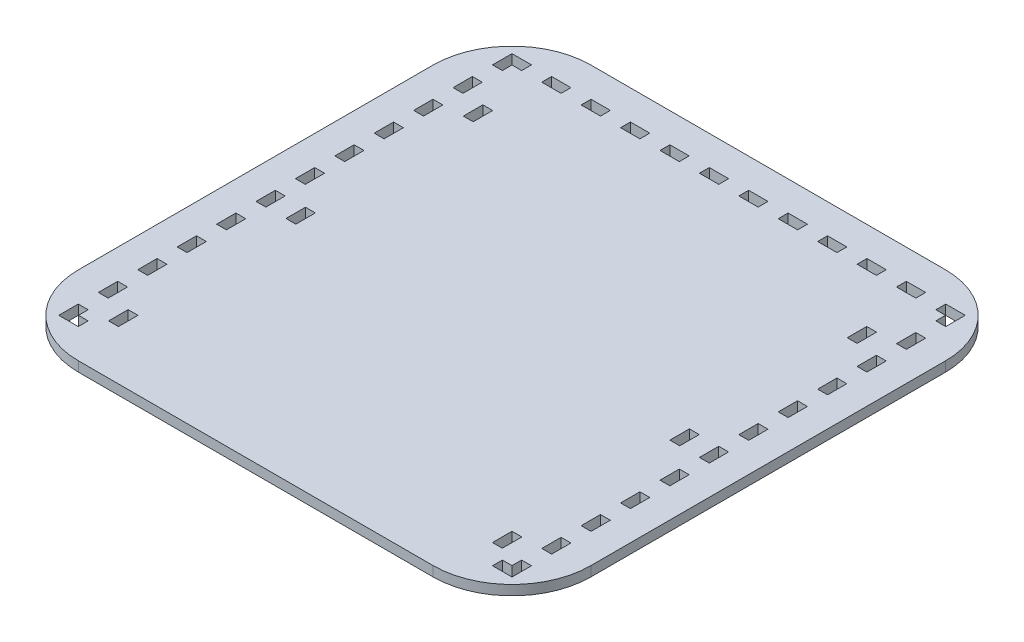
SolidWorks part; units mm, degrees
ref_plane "Front Plane" through (0, 0, 0) normal (0, 0, 1) x (1, 0, 0)
ref_plane "Top Plane" through (0, 0, 0) normal (0, 1, 0) x (1, 0, 0)
ref_plane "Right Plane" through (0, 0, 0) normal (1, 0, 0) x (0, 0, -1)
sketch "Sketch1" plane through (0, 0, 0) normal (0, 1, 0) x (1, 0, 0)
  line L0 (133.477, -292.1) -> (133.477, 0) construction
  line L1 (-6.223, -241.173) -> (-12.573, -241.173)
  line L2 (-6.223, -228.727) -> (-6.223, -241.173)
  line L3 (-12.573, -228.727) -> (-6.223, -228.727)
  line L4 (-12.573, -241.173) -> (-12.573, -254.127) construction
  line L5 (-6.223, -215.773) -> (-12.573, -215.773)
  line L6 (-6.223, -203.327) -> (-6.223, -215.773)
  line L7 (-12.573, -203.327) -> (-6.223, -203.327)
  line L8 (-12.573, -215.773) -> (-12.573, -228.727) construction
  line L9 (-6.223, -190.373) -> (-12.573, -190.373)
  line L10 (-6.223, -177.927) -> (-6.223, -190.373)
  line L11 (-12.573, -177.927) -> (-6.223, -177.927)
  line L12 (-12.573, -190.373) -> (-12.573, -203.327) construction
  line L13 (-6.223, -164.973) -> (-12.573, -164.973)
  line L14 (-6.223, -152.527) -> (-6.223, -164.973)
  line L15 (-12.573, -152.527) -> (-6.223, -152.527)
  line L16 (-12.573, -164.973) -> (-12.573, -177.927) construction
  line L17 (-6.223, -139.573) -> (-12.573, -139.573)
  line L18 (-6.223, -127.127) -> (-6.223, -139.573)
  line L19 (-12.573, -127.127) -> (-6.223, -127.127)
  line L20 (-12.573, -139.573) -> (-12.573, -152.527) construction
  line L21 (-6.223, -114.173) -> (-12.573, -114.173)
  line L22 (-6.223, -101.727) -> (-6.223, -114.173)
  line L23 (-12.573, -101.727) -> (-6.223, -101.727)
  line L24 (-12.573, -114.173) -> (-12.573, -127.127) construction
  line L25 (-6.223, -88.773) -> (-12.573, -88.773)
  line L26 (-6.223, -76.327) -> (-6.223, -88.773)
  line L27 (-12.573, -76.327) -> (-6.223, -76.327)
  line L28 (-12.573, -88.773) -> (-12.573, -101.727) construction
  line L29 (-6.223, -63.373) -> (-12.573, -63.373)
  line L30 (-6.223, -50.927) -> (-6.223, -63.373)
  line L31 (-12.573, -50.927) -> (-6.223, -50.927)
  line L32 (-12.573, -63.373) -> (-12.573, -76.327) construction
  line L33 (-6.223, -37.973) -> (-12.573, -37.973)
  line L34 (-6.223, -25.527) -> (-6.223, -37.973)
  line L35 (-12.573, -25.527) -> (-6.223, -25.527)
  line L36 (-12.573, -37.973) -> (-12.573, -50.927) construction
  line L37 (-6.223, -12.573) -> (-12.573, -12.573)
  line L38 (-6.223, -12.573) -> (-6.223, -6.35)
  line L39 (-6.223, -6.35) -> (0, -6.35)
  line L40 (-12.573, -12.573) -> (-12.573, -25.527) construction
  line L41 (0, -6.35) -> (0, 0)
  line L42 (273.177, -285.75) -> (273.177, -279.527)
  line L43 (273.177, -279.527) -> (279.527, -279.527)
  line L44 (279.527, -279.527) -> (279.527, -266.573) construction
  line L45 (279.527, -266.573) -> (273.177, -266.573)
  line L46 (273.177, -266.573) -> (273.177, -254.127)
  line L47 (273.177, -254.127) -> (279.527, -254.127)
  line L48 (279.527, -254.127) -> (279.527, -241.173) construction
  line L49 (12.954, -292.1) -> (12.954, -307.975) construction
  line L50 (279.527, -241.173) -> (273.177, -241.173)
  line L51 (-6.223, -279.527) -> (-6.223, -285.75)
  line L52 (-12.573, -279.527) -> (-6.223, -279.527)
  line L53 (-12.573, -266.573) -> (-12.573, -279.527) construction
  line L54 (-6.223, -266.573) -> (-12.573, -266.573)
  line L55 (-6.223, -254.127) -> (-6.223, -266.573)
  line L56 (-12.573, -254.127) -> (-6.223, -254.127)
  line L57 (273.177, -241.173) -> (273.177, -228.727)
  line L58 (273.177, -228.727) -> (279.527, -228.727)
  line L59 (279.527, -228.727) -> (279.527, -215.773) construction
  line L60 (279.527, -215.773) -> (273.177, -215.773)
  line L61 (273.177, -215.773) -> (273.177, -203.327)
  line L62 (273.177, -203.327) -> (279.527, -203.327)
  line L63 (279.527, -203.327) -> (279.527, -190.373) construction
  line L64 (279.527, -190.373) -> (273.177, -190.373)
  line L65 (273.177, -190.373) -> (273.177, -177.927)
  line L66 (273.177, -177.927) -> (279.527, -177.927)
  line L67 (279.527, -177.927) -> (279.527, -164.973) construction
  line L68 (279.527, -164.973) -> (273.177, -164.973)
  line L69 (273.177, -164.973) -> (273.177, -152.527)
  line L70 (273.177, -152.527) -> (279.527, -152.527)
  line L71 (279.527, -152.527) -> (279.527, -139.573) construction
  line L72 (279.527, -139.573) -> (273.177, -139.573)
  line L73 (273.177, -139.573) -> (273.177, -127.127)
  line L74 (273.177, -127.127) -> (279.527, -127.127)
  line L75 (279.527, -127.127) -> (279.527, -114.173) construction
  line L76 (279.527, -114.173) -> (273.177, -114.173)
  line L77 (273.177, -114.173) -> (273.177, -101.727)
  line L78 (273.177, -101.727) -> (279.527, -101.727)
  line L79 (279.527, -101.727) -> (279.527, -88.773) construction
  line L80 (279.527, -88.773) -> (273.177, -88.773)
  line L81 (273.177, -88.773) -> (273.177, -76.327)
  line L82 (273.177, -76.327) -> (279.527, -76.327)
  line L83 (279.527, -76.327) -> (279.527, -63.373) construction
  line L84 (279.527, -63.373) -> (273.177, -63.373)
  line L85 (273.177, -63.373) -> (273.177, -50.927)
  line L86 (273.177, -50.927) -> (279.527, -50.927)
  line L87 (279.527, -50.927) -> (279.527, -37.973) construction
  line L88 (279.527, -37.973) -> (273.177, -37.973)
  line L89 (273.177, -37.973) -> (273.177, -25.527)
  line L90 (273.177, -25.527) -> (279.527, -25.527)
  line L91 (279.527, -25.527) -> (279.527, -12.573) construction
  line L92 (279.527, -12.573) -> (273.177, -12.573)
  line L93 (273.177, -12.573) -> (273.177, -6.35)
  line L94 (273.177, -6.35) -> (266.954, -6.35)
  line L95 (266.954, -6.35) -> (266.954, 0)
  line L96 (0, 0) -> (12.954, 0) construction
  line L97 (12.954, 0) -> (12.954, -6.35)
  line L98 (12.954, -6.35) -> (25.4, -6.35)
  line L99 (25.4, -6.35) -> (25.4, 0)
  line L100 (25.4, 0) -> (38.354, 0) construction
  line L101 (38.354, 0) -> (38.354, -6.35)
  line L102 (38.354, -6.35) -> (50.8, -6.35)
  line L103 (50.8, -6.35) -> (50.8, 0)
  line L104 (50.8, 0) -> (63.754, 0) construction
  line L105 (63.754, 0) -> (63.754, -6.35)
  line L106 (63.754, -6.35) -> (76.2, -6.35)
  line L107 (76.2, -6.35) -> (76.2, 0)
  line L108 (76.2, 0) -> (89.154, 0) construction
  line L109 (89.154, 0) -> (89.154, -6.35)
  line L110 (89.154, -6.35) -> (101.6, -6.35)
  line L111 (101.6, -6.35) -> (101.6, 0)
  line L112 (101.6, 0) -> (114.554, 0) construction
  line L113 (114.554, 0) -> (114.554, -6.35)
  line L114 (114.554, -6.35) -> (127, -6.35)
  line L115 (127, -6.35) -> (127, 0)
  line L116 (127, 0) -> (139.954, 0) construction
  line L117 (139.954, 0) -> (139.954, -6.35)
  line L118 (139.954, -6.35) -> (152.4, -6.35)
  line L119 (152.4, -6.35) -> (152.4, 0)
  line L120 (152.4, 0) -> (165.354, 0) construction
  line L121 (165.354, 0) -> (165.354, -6.35)
  line L122 (165.354, -6.35) -> (177.8, -6.35)
  line L123 (177.8, -6.35) -> (177.8, 0)
  line L124 (177.8, 0) -> (190.754, 0) construction
  line L125 (190.754, 0) -> (190.754, -6.35)
  line L126 (190.754, -6.35) -> (203.2, -6.35)
  line L127 (203.2, -6.35) -> (203.2, 0)
  line L128 (203.2, 0) -> (216.154, 0) construction
  line L129 (216.154, 0) -> (216.154, -6.35)
  line L130 (216.154, -6.35) -> (228.6, -6.35)
  line L131 (228.6, -6.35) -> (228.6, 0)
  line L132 (228.6, 0) -> (241.554, 0) construction
  line L133 (241.554, 0) -> (241.554, -6.35)
  line L134 (241.554, -6.35) -> (254, -6.35)
  line L135 (254, -6.35) -> (254, 0)
  line L136 (254, 0) -> (266.954, 0) construction
  line L137 (16.129, -311.15) -> (250.825, -311.15) construction
  line L138 (254, -313.784) -> (254, -292.1) construction
  line L139 (165.227, -152.4635) -> (171.577, -152.4635) construction
  line L140 (165.227, -266.7635) -> (171.577, -266.7635) construction
  line L141 (165.227, -266.7635) -> (165.227, -279.3365) construction
  line L142 (165.227, -279.3365) -> (171.577, -279.3365) construction
  line L143 (171.577, -266.7635) -> (171.577, -279.3365) construction
  line L144 (165.227, -152.4635) -> (165.227, -165.0365) construction
  line L145 (165.227, -165.0365) -> (171.577, -165.0365) construction
  line L146 (171.577, -152.4635) -> (171.577, -165.0365) construction
  line L147 (165.227, -38.1635) -> (171.577, -38.1635) construction
  line L148 (165.227, -38.1635) -> (165.227, -50.7365) construction
  line L149 (165.227, -50.7365) -> (171.577, -50.7365) construction
  line L150 (-6.223, -285.75) -> (0, -285.75)
  line L151 (0, -285.75) -> (0, -292.1)
  line L152 (0, -292.1) -> (12.954, -292.1) construction
  line L153 (171.577, -38.1635) -> (171.577, -50.7365) construction
  line L154 (254, -152.273) -> (260.35, -152.273)
  line L155 (254, -266.573) -> (260.35, -266.573)
  line L156 (254, -266.573) -> (254, -279.146)
  line L157 (254, -279.146) -> (260.35, -279.146)
  line L158 (260.35, -266.573) -> (260.35, -279.146)
  line L159 (254, -152.273) -> (254, -164.846)
  line L160 (254, -292.1) -> (266.954, -292.1) construction
  line L161 (266.954, -292.1) -> (266.954, -285.75)
  line L162 (266.954, -285.75) -> (273.177, -285.75)
  line L163 (254, -164.846) -> (260.35, -164.846)
  line L164 (260.35, -152.273) -> (260.35, -164.846)
  line L165 (254, -37.973) -> (260.35, -37.973)
  line L166 (254, -37.973) -> (254, -50.546)
  line L167 (254, -50.546) -> (260.35, -50.546)
  line L168 (260.35, -37.973) -> (260.35, -50.546)
  line L169 (-12.573, -0.127) -> (-6.223, -0.127) [skipped]
  line L170 (-6.223, -0.127) -> (-6.223, -12.573) [skipped]
  line L171 (273.177, -12.573) -> (273.177, -0.127) [skipped]
  line L172 (6.604, -37.973) -> (6.604, -50.546)
  line L173 (12.954, -50.546) -> (6.604, -50.546)
  line L174 (12.954, -37.973) -> (12.954, -50.546)
  line L175 (12.954, -37.973) -> (6.604, -37.973)
  line L176 (6.604, -152.273) -> (6.604, -164.846)
  line L177 (12.954, -164.846) -> (6.604, -164.846)
  line L178 (12.954, -152.273) -> (12.954, -164.846)
  line L179 (6.604, -266.573) -> (6.604, -279.146)
  line L180 (12.954, -279.146) -> (6.604, -279.146)
  line L181 (12.954, -266.573) -> (12.954, -279.146)
  line L182 (12.954, -266.573) -> (6.604, -266.573)
  line L183 (12.954, -152.273) -> (6.604, -152.273)
  line L184 (-12.573, -146.05) -> (279.527, -146.05) construction
  line L185 (-12.573, -25.527) -> (-12.573, -37.973)
  line L186 (19.177, -311.15) -> (247.777, -311.15)
  line L187 (-31.623, -260.35) -> (-31.623, -31.75)
  line L188 (19.177, 19.05) -> (247.777, 19.05)
  line L189 (298.577, -260.35) -> (298.577, -31.75)
  line L190 (-31.623, -311.15) -> (298.577, 19.05) construction
  line L191 (-31.623, 19.05) -> (298.577, -311.15) construction
  line L192 (-12.573, -50.927) -> (-12.573, -63.373)
  line L193 (-12.573, -76.327) -> (-12.573, -88.773)
  line L194 (-12.573, -101.727) -> (-12.573, -114.173)
  line L195 (-12.573, -127.127) -> (-12.573, -139.573)
  line L196 (-12.573, -152.527) -> (-12.573, -164.973)
  line L197 (-12.573, -177.927) -> (-12.573, -190.373)
  line L198 (-12.573, -203.327) -> (-12.573, -215.773)
  line L199 (-12.573, -228.727) -> (-12.573, -241.173)
  line L200 (-12.573, -254.127) -> (-12.573, -266.573)
  line L201 (-12.573, -279.527) -> (-12.573, -292.1)
  line L202 (-12.573, -292.1) -> (0, -292.1)
  line L203 (266.954, -292.1) -> (279.527, -292.1)
  line L204 (279.527, -292.1) -> (279.527, -279.527)
  line L205 (279.527, -254.127) -> (279.527, -266.573)
  line L206 (279.527, -241.173) -> (279.527, -228.727)
  line L207 (279.527, -203.327) -> (279.527, -215.773)
  line L208 (279.527, -177.927) -> (279.527, -190.373)
  line L209 (279.527, -152.527) -> (279.527, -164.973)
  line L210 (279.527, -127.127) -> (279.527, -139.573)
  line L211 (279.527, -101.727) -> (279.527, -114.173)
  line L212 (279.527, -76.327) -> (279.527, -88.773)
  line L213 (279.527, -50.927) -> (279.527, -63.373)
  line L214 (279.527, -25.527) -> (279.527, -37.973)
  line L215 (279.527, -12.573) -> (279.527, 0)
  line L216 (279.527, 0) -> (266.954, 0)
  line L217 (241.554, 0) -> (254, 0)
  line L218 (216.154, 0) -> (228.6, 0)
  line L219 (190.754, 0) -> (203.2, 0)
  line L220 (177.8, 0) -> (165.354, 0)
  line L221 (152.4, 0) -> (139.954, 0)
  line L222 (127, 0) -> (114.554, 0)
  line L223 (101.6, 0) -> (89.154, 0)
  line L224 (76.2, 0) -> (63.754, 0)
  line L225 (50.8, 0) -> (38.354, 0)
  line L226 (25.4, 0) -> (12.954, 0)
  line L227 (0, 0) -> (-12.573, 0)
  line L228 (-12.573, 0) -> (-12.573, -12.573)
  arc A1 (12.954, -307.975) -> (16.129, -311.15) centre (16.129, -307.975) ccw construction
  arc A2 (247.777, 19.05) -> (298.577, -31.75) centre (247.777, -31.75) cw
  arc A3 (247.777, -311.15) -> (298.577, -260.35) centre (247.777, -260.35) ccw
  arc A4 (19.177, -311.15) -> (-31.623, -260.35) centre (19.177, -260.35) cw
  arc A5 (-31.623, -31.75) -> (19.177, 19.05) centre (19.177, -31.75) cw
  point P195 (133.477, -146.05)
  dimension "D45" = 50.8
  dimension "D4" = 12.954
  dimension "D6" = 6.35
  dimension "D7" = 11
  dimension "D8" = 6.223
  dimension "D9" = 12.954
  dimension "D10" = 19.05
  dimension "D11" = 6.223
  dimension "D12" = 6.35
  dimension "D14" = 82.423
  dimension "D15" = 6.223
  dimension "D16" = 12.954
  dimension "D17" = 6.35
  dimension "D18" = 6.223
  dimension "D5" = 12.446
  dimension "D19" = 6.223
  dimension "D20" = 6.35
  dimension "D21" = 12.446
  dimension "D22" = 12.954
  dimension "D23" = 6.35
  dimension "D24" = 6.35
  dimension "D25" = 6.223
  dimension "D27" = 6.223
  dimension "D28" = 6.223
  dimension "D29" = 6.35
  dimension "D30" = 12.954
  dimension "D31" = 12.446
  dimension "D32" = 6.35
  dimension "D33" = 10
  dimension "D34" = 0
  dimension "D35" = 0
  dimension "D36" = 12.573
  dimension "D37" = 12.7635
  dimension "D39" = 6.35
  dimension "D40" = 12.573
  dimension "D41" = 12.954
  dimension "D43" = 330.2
  dimension "D44" = 330.2
  dimension "D26" = 11
  dimension "D38" = 3
  dimension "D42" = 3
extrude "Boss-Extrude1" add sketch "Sketch1" along normal blind 6.35
